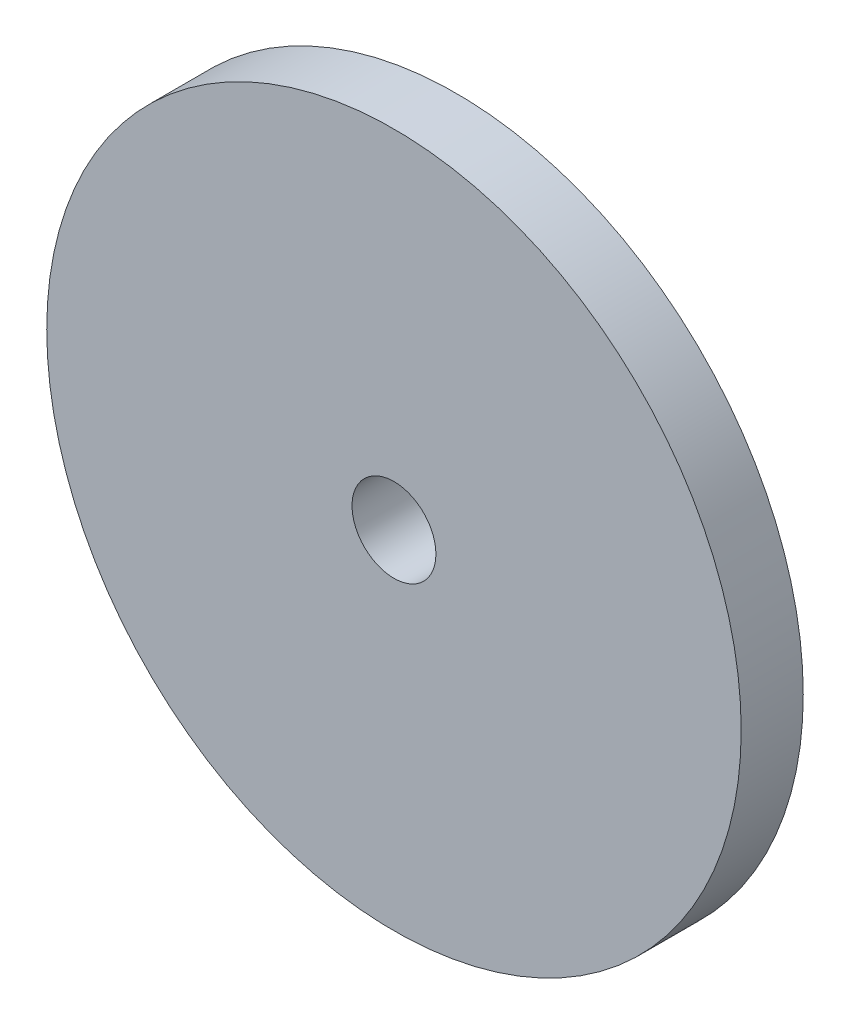
SolidWorks part; units mm, degrees
ref_plane "Alzado" through (0, 0, 0) normal (0, 0, 1) x (1, 0, 0)
ref_plane "Planta" through (0, 0, 0) normal (0, 1, 0) x (1, 0, 0)
ref_plane "Vista lateral" through (0, 0, 0) normal (1, 0, 0) x (0, 0, -1)
sketch "Model" plane through (0, 0, 0) normal (0, 0, 1) x (1, 0, 0)
  circle A0 centre (36.636, 18.676) radius 2.0277
  circle A1 centre (36.636, 18.676) radius 16.7837
extrude "Saliente-Extruir1" add sketch "Model" along normal blind 3
